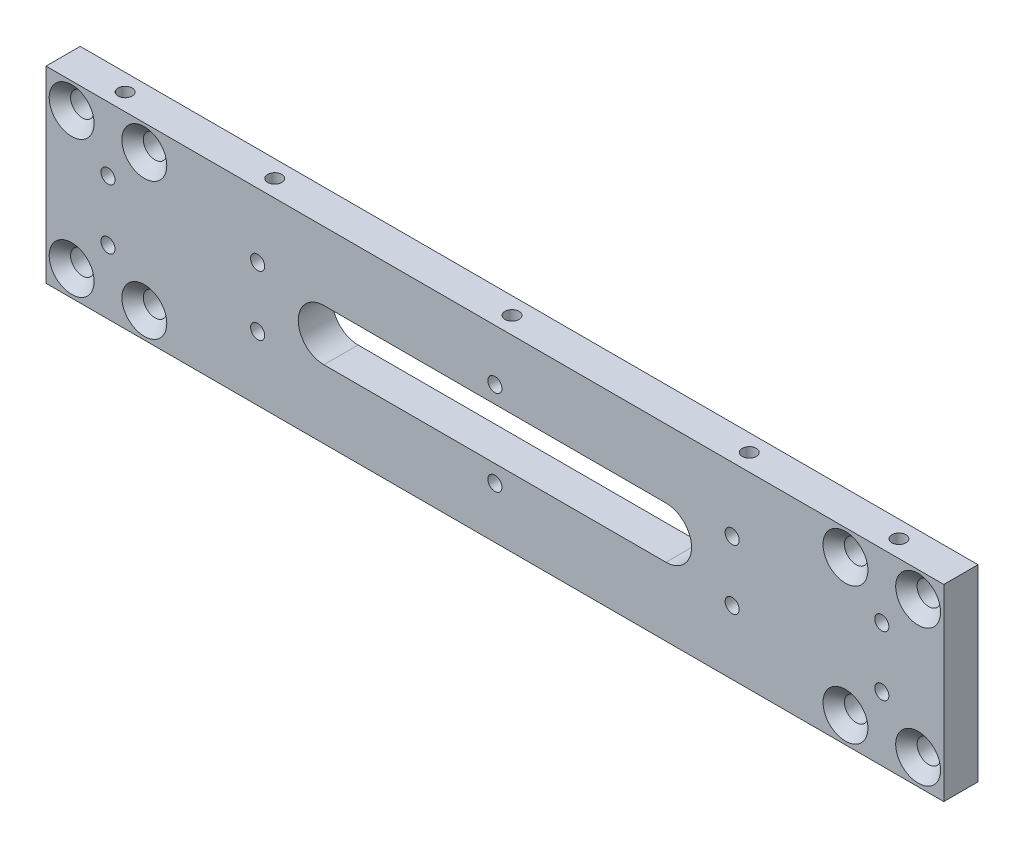
SolidWorks part; units mm, degrees
ref_plane "Plan de face" through (0, 0, 0) normal (0, 0, 1) x (1, 0, 0)
ref_plane "Plan de dessus" through (0, 0, 0) normal (0, 1, 0) x (1, 0, 0)
ref_plane "Plan de droite" through (0, 0, 0) normal (1, 0, 0) x (0, 0, -1)
sketch "Esquisse1" plane through (0, 0, 0) normal (0, 0, 1) x (1, 0, 0)
  line L1 (-73.1443, 11.1594) -> (136.8557, 11.1594)
  line L2 (-73.1443, 11.1594) -> (-73.1443, -32.8406)
  line L3 (-73.1443, -32.8406) -> (136.8557, -32.8406)
  line L4 (136.8557, 11.1594) -> (136.8557, -32.8406)
  dimension "D1" = 210
  dimension "D2" = 44
extrude "Boss.-Extru.1" add sketch "Esquisse1" along normal blind 8
sketch "Esquisse2" plane through (0, 0, 8) normal (0, 0, 1) x (1, 0, 0)
  line L0 (136.8557, 11.1594) -> (-73.1443, 11.1594) construction
  line L1 (-73.1443, 11.1594) -> (-73.1443, -32.8406) construction
  line L2 (-73.1443, -32.8406) -> (136.8557, -32.8406) construction
  line L3 (136.8557, -32.8406) -> (136.8557, 11.1594) construction
  circle A0 centre (-67.1443, 5.1594) radius 2.75
  circle A1 centre (-67.1443, -26.8406) radius 2.75
  circle A2 centre (-50.1443, 5.1594) radius 2.75
  circle A3 centre (-50.1443, -26.8406) radius 2.75
  circle A4 centre (130.8557, 5.1594) radius 2.75
  circle A5 centre (130.8557, -26.8406) radius 2.75
  circle A6 centre (113.8557, 5.1594) radius 2.75
  circle A7 centre (113.8557, -26.8406) radius 2.75
  dimension "D1" = 5.5
  dimension "D2" = 6
  dimension "D3" = 6
  dimension "D4" = 6
  dimension "D5" = 6
  dimension "D6" = 5.5
  dimension "D7" = 5.5
  dimension "D8" = 17
  dimension "D9" = 5.5
  dimension "D10" = 6
  dimension "D11" = 17
  dimension "D12" = 5.5
  dimension "D13" = 6
  dimension "D14" = 6
  dimension "D15" = 5.5
  dimension "D16" = 6
  dimension "D18" = 6
  dimension "D19" = 17
  dimension "D20" = 5.5
  dimension "D21" = 5.5
  dimension "D22" = 17
  dimension "D23" = 6
  dimension "D17" = 6
extrude "Enlèv. mat.-Extru.1" cut sketch "Esquisse2" against normal through all
chamfer "Chanfrein1" distance 2.5 angle 45 8 edges at (-64.3943, 5.1594, 8) (-47.3943, -26.8406, 8) (-64.3943, -26.8406, 8) (116.6057, -26.8406, 8) (133.6057, -26.8406, 8) (133.6057, 5.1594, 8) (116.6057, 5.1594, 8) (-47.3943, 5.1594, 8)
sketch "Esquisse3" plane through (0, 0, 8) normal (0, 0, 1) x (1, 0, 0)
  line L0 (-8.1443, -10.8406) -> (71.8557, -10.8406) construction
  line L1 (-8.1443, -4.8406) -> (71.8557, -4.8406)
  line L2 (-8.1443, -16.8406) -> (71.8557, -16.8406)
  line L3 (136.8557, 11.1594) -> (-73.1443, 11.1594) construction
  line L4 (136.8557, -32.8406) -> (136.8557, 11.1594) construction
  arc A0 (-8.1443, -4.8406) -> (-8.1443, -16.8406) centre (-8.1443, -10.8406) ccw
  arc A1 (71.8557, -16.8406) -> (71.8557, -4.8406) centre (71.8557, -10.8406) ccw
  point P2 (31.8557, -10.8406)
  dimension "D1" = 22
  dimension "D2" = 105
  dimension "D3" = 12
extrude "Enlèv. mat.-Extru.2" cut sketch "Esquisse3" against normal through all
sketch "Esquisse4" plane through (0, 0, 8) normal (0, 0, 1) x (1, 0, 0)
  line L0 (-73.1443, -32.8406) -> (136.8557, -32.8406) construction
  line L1 (-73.1443, 11.1594) -> (-73.1443, -32.8406) construction
  line L2 (136.8557, 11.1594) -> (-73.1443, 11.1594) construction
  line L4 (136.8557, -32.8406) -> (136.8557, 11.1594) construction
  circle A0 centre (-58.6443, -17.8406) radius 1.65
  circle A1 centre (-58.6443, -3.8406) radius 1.65
  circle A2 centre (-23.6443, -3.8406) radius 1.65
  circle A3 centre (-23.6443, -17.8406) radius 1.65
  circle A4 centre (87.3557, -3.8406) radius 1.65
  circle A5 centre (87.3557, -17.8406) radius 1.65
  circle A6 centre (122.3557, -3.8406) radius 1.65
  circle A7 centre (122.3557, -17.8406) radius 1.65
  circle A8 centre (31.8557, -0.8406) radius 1.65
  circle A9 centre (31.8557, -20.8406) radius 1.65
  dimension "D1" = 3.3
  dimension "D2" = 15
  dimension "D3" = 14.5
  dimension "D4" = 3.3
  dimension "D5" = 15
  dimension "D6" = 14.5
  dimension "D9" = 3.3
  dimension "D10" = 35
  dimension "D12" = 14.5
  dimension "D13" = 35
  dimension "D16" = 3.3
  dimension "D17" = 12
  dimension "D18" = 105
  dimension "D14" = 12
  dimension "D15" = 105
  dimension "D7" = 2
  dimension "D8" = 2
  dimension "D11" = 2
extrude "Enlèv. mat.-Extru.3" cut sketch "Esquisse4" against normal through all
sketch "Esquisse5" plane through (0, 11.1594, 0) normal (0, 1, 0) x (1, 0, 0)
  line L0 (136.8557, 0) -> (-73.1443, 0) construction
  line L1 (-73.1443, -8) -> (-73.1443, 0) construction
  line L2 (136.8557, -8) -> (136.8557, 0) construction
  circle A0 centre (-58.6443, -4) radius 1.65
  circle A1 centre (-23.6443, -4) radius 1.65
  circle A2 centre (87.3557, -4) radius 1.65
  circle A3 centre (122.3557, -4) radius 1.65
  circle A4 centre (31.8557, -4) radius 1.65
  dimension "D1" = 3.3
  dimension "D7" = 2
  dimension "D8" = 14.5
  dimension "D9" = 35
  dimension "D10" = 55.5
  dimension "D11" = 55.5
  dimension "D2" = 4
  dimension "D3" = 14.5
  dimension "D4" = 2
  dimension "D5" = 2
  dimension "D6" = 2
extrude "Enlèv. mat.-Extru.4" cut sketch "Esquisse5" against normal blind 8
sketch "Esquisse6" plane through (0, -32.8406, 0) normal (0, -1, 0) x (1, 0, 0)
  line L0 (-73.1443, 0) -> (136.8557, 0) construction
  line L1 (-73.1443, 8) -> (-73.1443, 0) construction
  circle A0 centre (-58.6443, 4) radius 1.65
  circle A1 centre (-23.6443, 4) radius 1.65
  circle A2 centre (87.3557, 4) radius 1.65
  circle A3 centre (122.3557, 4) radius 1.65
  circle A4 centre (31.8557, 4) radius 1.65
  dimension "D1" = 3.3
  dimension "D2" = 4
  dimension "D3" = 14.5
  dimension "D7" = 35
  dimension "D10" = 35
  dimension "D11" = 55.5
  dimension "D12" = 55.5
  dimension "D8" = 14.5
  dimension "D4" = 2
  dimension "D5" = 2
  dimension "D6" = 2
  dimension "D9" = 2
extrude "Enlèv. mat.-Extru.5" cut sketch "Esquisse6" against normal blind 8
